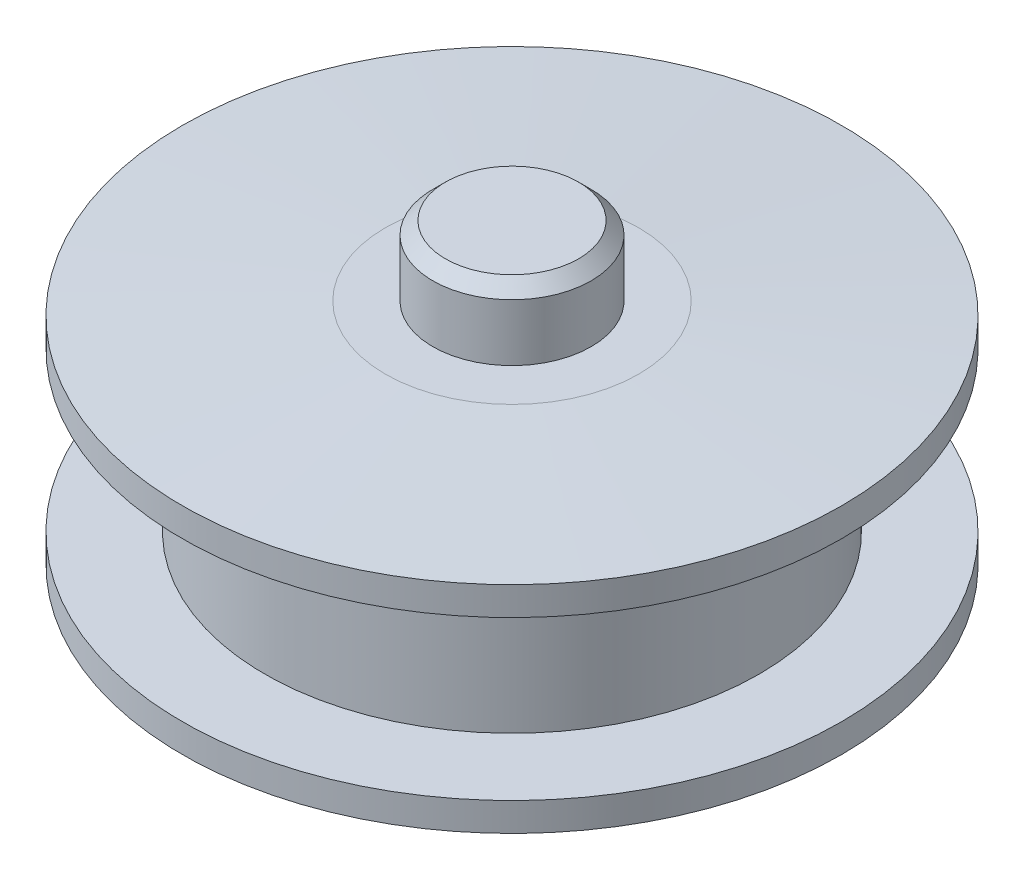
SolidWorks part; units mm, degrees
ref_plane "Front Plane" through (0, 0, 0) normal (0, 0, 1) x (1, 0, 0)
ref_plane "Top Plane" through (0, 0, 0) normal (0, 1, 0) x (1, 0, 0)
ref_plane "Right Plane" through (0, 0, 0) normal (1, 0, 0) x (0, 0, -1)
sketch "Sketch1" plane through (0, 0, 0) normal (0, 0, 1) x (1, 0, 0)
  line L0 (1.05, 3) -> (0, 3)
  line L1 (0, 3) -> (0, -3)
  line L2 (0, -3) -> (1.05, -3)
  line L3 (1.05, -3) -> (1.25, -2.8)
  line L4 (1.25, -2.8) -> (1.25, -1.9)
  line L5 (1.25, -1.9) -> (2, -1.9)
  line L6 (2, -1.9) -> (5.2, -1.7)
  line L7 (5.2, -1.7) -> (5.2, -1.25)
  line L8 (5.2, -1.25) -> (3.9, -1.25)
  line L9 (3.9, -1.25) -> (3.9, 1.25)
  line L10 (3.9, 1.25) -> (5.2, 1.25)
  line L11 (5.2, 1.25) -> (5.2, 1.7)
  line L12 (5.2, 1.7) -> (2, 1.9)
  line L13 (2, 1.9) -> (1.25, 1.9)
  line L14 (1.25, 1.9) -> (1.25, 2.8)
  line L15 (1.25, 2.8) -> (1.05, 3)
  line L16 (0, 3) -> (0, -3) construction
revolve "Revolve1" add sketch "Sketch1" angle 360 about L16
